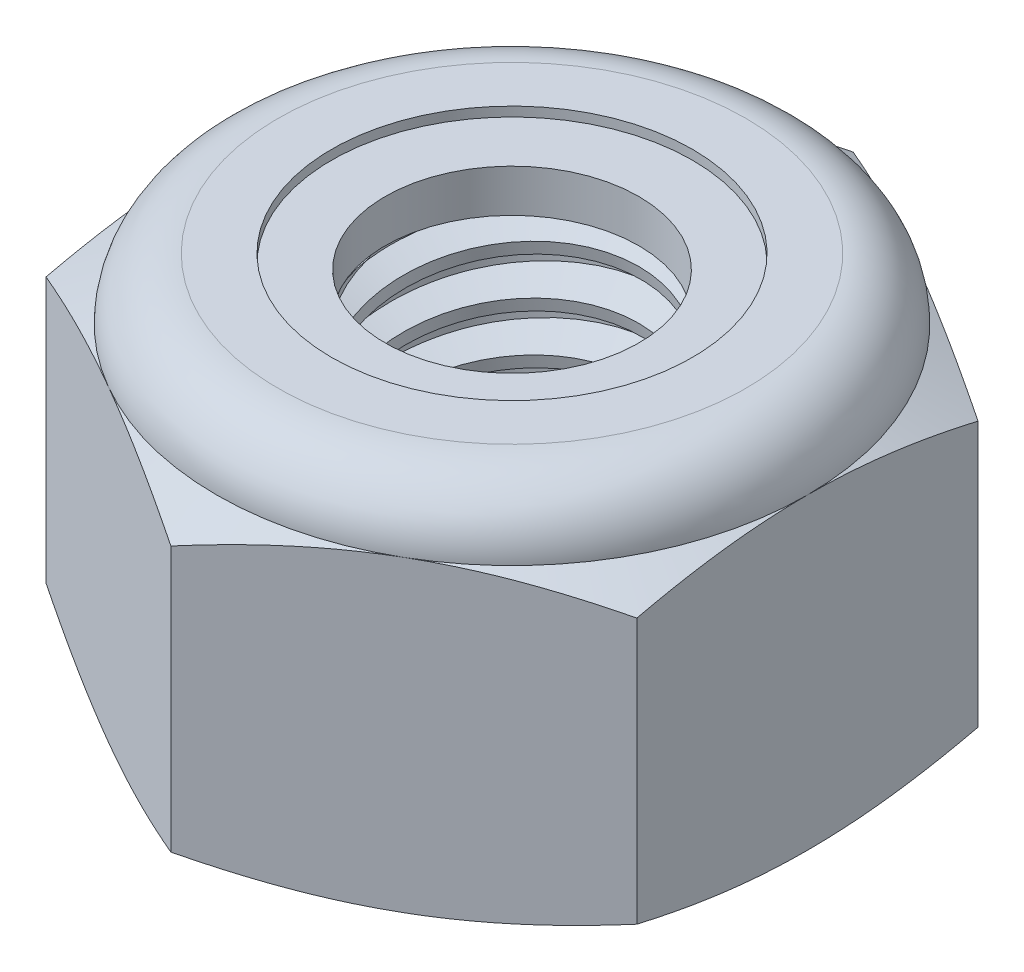
SolidWorks part; units mm, degrees
material "Cast Alloy Steel"
ref_plane "Front" through (0, 0, 0) normal (0, 0, 1) x (1, 0, 0)
ref_plane "Top" through (0, 0, 0) normal (0, 1, 0) x (1, 0, 0)
ref_plane "Right" through (0, 0, 0) normal (1, 0, 0) x (0, 0, -1)
sketch "Sketch1" plane through (0, 0, 0) normal (0, 1, 0) x (1, 0, 0)
  line L1 (0, 5.4993) -> (-4.7625, 2.7496)
  line L2 (-4.7625, 2.7496) -> (-4.7625, -2.7496)
  line L3 (-4.7625, -2.7496) -> (0, -5.4993)
  line L4 (0, -5.4993) -> (4.7625, -2.7496)
  line L5 (4.7625, -2.7496) -> (4.7625, 2.7496)
  line L6 (4.7625, 2.7496) -> (0, 5.4993)
  circle A0 centre (0, 0) radius 4.7625 construction
  dimension "Hex Flats" = 9.525
extrude "Extrude1" add sketch "Sketch1" along normal blind 5.9531
sketch "Sketch2" plane through (0, 0, 0) normal (1, 0, 0) x (0, 0, -1)
  line L0 (-2.413, 0) -> (-2.413, 5.9531) construction
  line L1 (0, 0) -> (2.413, 0)
  line L2 (0, 0) -> (0, 5.9531)
  line L3 (0, 5.9531) -> (2.413, 5.9531)
  line L4 (2.413, 0) -> (2.413, 5.9531)
  line L5 (-2.7496, 5.9531) -> (2.7496, 5.9531) construction
  line L7 (0, -2.413) -> (0, 0) construction
  dimension "Thread Dia" = 4.826
revolve "Revolve1" add sketch "Sketch2" angle 360 about L7
sketch "Sketch3" plane through (0, 0, 0) normal (1, 0, 0) x (0, 0, -1)
  line L0 (2.413, 5.9531) -> (-2.413, 5.9531) construction
  line L1 (-2.413, 5.9531) -> (-2.413, 5.1594) construction
  line L2 (-2.413, 5.1594) -> (2.413, 5.9531) construction
  line L3 (2.413, 5.9531) -> (2.4291, 5.8552) construction
  line L4 (2.4291, 5.8552) -> (2.5418, 5.1699)
  line L5 (2.5418, 5.1699) -> (2.0776, 5.3449)
  line L6 (2.0776, 5.3449) -> (2.0454, 5.5407)
  line L7 (2.0454, 5.5407) -> (2.4291, 5.8552)
  line L8 (2.0615, 5.4428) -> (2.4855, 5.5126) construction
  line L9 (2.413, 5.9531) -> (2.413, 5.5006) construction
  line L10 (2.413, 5.5006) -> (-2.413, 4.7069) construction
  line L11 (-2.413, 4.7069) -> (-2.413, 5.1594) construction
  line L12 (-0.1397, 5.9531) -> (0.1397, 4.2544) construction
  line L13 (-2.413, 0) -> (-2.413, 5.9531) construction
  line L14 (0, 5.9531) -> (2.413, 5.9531) construction
  line L15 (2.413, 0) -> (2.413, 5.9531) construction
  point P13 (0, 5.1038)
  dimension "D1" = 0.0992
  dimension "D2" = 0.1984
  dimension "Thread Pitch" = 0.7937
  dimension "D4" = 60
  dimension "D5" = 0.7937
revolve "Cut-Revolve1" cut sketch "Sketch3" angle 360 about L12
pattern_linear "LPattern1" count 8 spacing 0.7937 along (0, -1, 0) count 2 spacing 0.7937 along (0, 1, 0) of "Cut-Revolve1"
sketch "Sketch4" plane through (0, 0, 0) normal (1, 0, 0) x (0, 0, -1)
  line L0 (0, 5.9531) -> (2.413, 5.9531)
  line L1 (2.413, 5.9531) -> (2.0454, 5.7817)
  line L2 (2.0454, 5.7817) -> (2.0454, 0.1714)
  line L3 (2.0454, 0.1714) -> (2.413, 0)
  line L4 (2.413, 0) -> (0, 0)
  line L5 (0, 0) -> (0, 5.9531)
  line L6 (2.413, 0) -> (2.413, 5.9531) construction
  line L7 (0, 5.9531) -> (2.413, 5.9531) construction
  line L8 (0, 0) -> (2.413, 0) construction
  line L9 (0, 0) -> (0, 5.9531) construction
  line L10 (0, 5.9531) -> (0, 6.3587) construction
  dimension "D1" = 25
revolve "Cut-Revolve2" cut sketch "Sketch4" angle 360 about L10
combine bodies "Combine1" operation type subtract main body 112 bodies to subtract 111
sketch "Sketch5" plane through (0, 0, 0) normal (1, 0, 0) x (0, 0, -1)
  line L0 (0, 0) -> (4.7625, 0)
  line L1 (4.7625, 0) -> (5.4993, 0.3436)
  line L2 (5.4993, 0.3436) -> (5.4993, 4.6174)
  line L3 (5.4993, 4.6174) -> (4.7625, 4.9609)
  line L4 (3.7703, 5.9531) -> (3.7703, 7.2231)
  line L5 (3.7703, 7.2231) -> (6.7693, 7.2231)
  line L6 (6.7693, 7.2231) -> (6.7693, -1.27)
  line L7 (6.7693, -1.27) -> (0, -1.27)
  line L8 (0, -1.27) -> (0, 0)
  line L9 (4.7625, 4.9609) -> (4.7625, 0) construction
  line L10 (0, 0) -> (2.413, 0) construction
  line L13 (5.4993, 2.4805) -> (6.7693, 2.4805) construction
  line L14 (5.4993, 5.9531) -> (5.4993, 0) construction
  line L15 (0, 0) -> (0, 7.2231) construction
  line L20 (0, 7.2231) -> (3.7703, 7.2231) construction
  line L22 (0, 5.9531) -> (2.413, 5.9531) construction
  arc A0 (4.7625, 4.9609) -> (3.7703, 5.9531) centre (3.7703, 4.9609) ccw
  dimension "D1" = 25
  dimension "D2" = 1.27
  dimension "D3" = 5.9531
  dimension "D4" = 0.9922
revolve "Cut-Revolve3" cut sketch "Sketch5" angle 360 about L15
sketch "Sketch6" plane through (0, 0, 0) normal (1, 0, 0) x (0, 0, -1)
  line L0 (0, 4.9609) -> (4.6101, 4.9609)
  line L1 (3.7703, 5.8007) -> (2.9079, 5.8007)
  line L2 (0, 7.2231) -> (0, 4.9609)
  line L3 (2.9079, 7.2231) -> (0, 7.2231)
  line L4 (0, 7.2231) -> (3.7703, 7.2231) construction
  line L5 (0, 0) -> (0, 7.2231) construction
  line L6 (0, 7.2231) -> (0, 44.323) construction
  line L7 (2.9079, 5.8007) -> (2.9079, 7.2231)
  line L8 (3.7703, 5.9531) -> (3.7703, 5.8007) construction
  line L9 (2.9079, 5.8007) -> (2.0454, 5.8007) construction
  line L10 (2.0454, 5.8007) -> (2.0454, 5.7817) construction
  arc A0 (4.6101, 4.9609) -> (3.7703, 5.8007) centre (3.7703, 4.9609) ccw
  arc A1 (4.7625, 4.9609) -> (3.7703, 5.9531) centre (3.7703, 4.9609) ccw construction
  dimension "D1" = 0.1524
revolve "Cut-Revolve4" cut sketch "Sketch6" angle 360 about L6
sketch "Sketch7" plane through (0, 0, 0) normal (1, 0, 0) x (0, 0, -1)
  line L0 (2.0454, 5.0371) -> (4.5301, 5.0371)
  line L1 (3.7703, 5.7245) -> (2.0454, 5.7245)
  line L2 (2.0454, 5.7245) -> (2.0454, 5.0371)
  line L3 (2.0454, 5.0371) -> (0, 5.0371) construction
  line L4 (0, 5.0371) -> (0, 5.7245) construction
  line L5 (0, 5.7245) -> (2.0454, 5.7245) construction
  line L6 (2.0454, 5.0371) -> (2.0454, 4.9609) construction
  line L7 (0, 4.9609) -> (4.6101, 4.9609) construction
  line L8 (3.7703, 5.7245) -> (3.7703, 5.8007) construction
  arc A0 (4.5301, 5.0371) -> (3.7703, 5.7245) centre (3.7703, 4.9609) ccw
  arc A2 (4.6101, 4.9609) -> (3.7703, 5.8007) centre (3.7703, 4.9609) ccw construction
  dimension "D1" = 0.0762
revolve "Revolve2" add sketch "Sketch7" angle 360 about L4
equation "\"D1@Sketch3\"=\"Thread Pitch@Sketch3\"/8"
equation "\"D2@Sketch3\"=\"Thread Pitch@Sketch3\"/4"
equation "\"D5@Sketch3\"=\"Thread Pitch@Sketch3\""
equation "\"D4@LPattern1\"=\"Thread Pitch@Sketch3\""
equation "\"D3@LPattern1\"=\"Thread Pitch@Sketch3\""
equation "\"D1@LPattern1\"=\"Height@Extrude1\"/\"Thread Pitch@Sketch3\""
equation "\"D4@Sketch5\"=\"Height@Extrude1\"/6"
